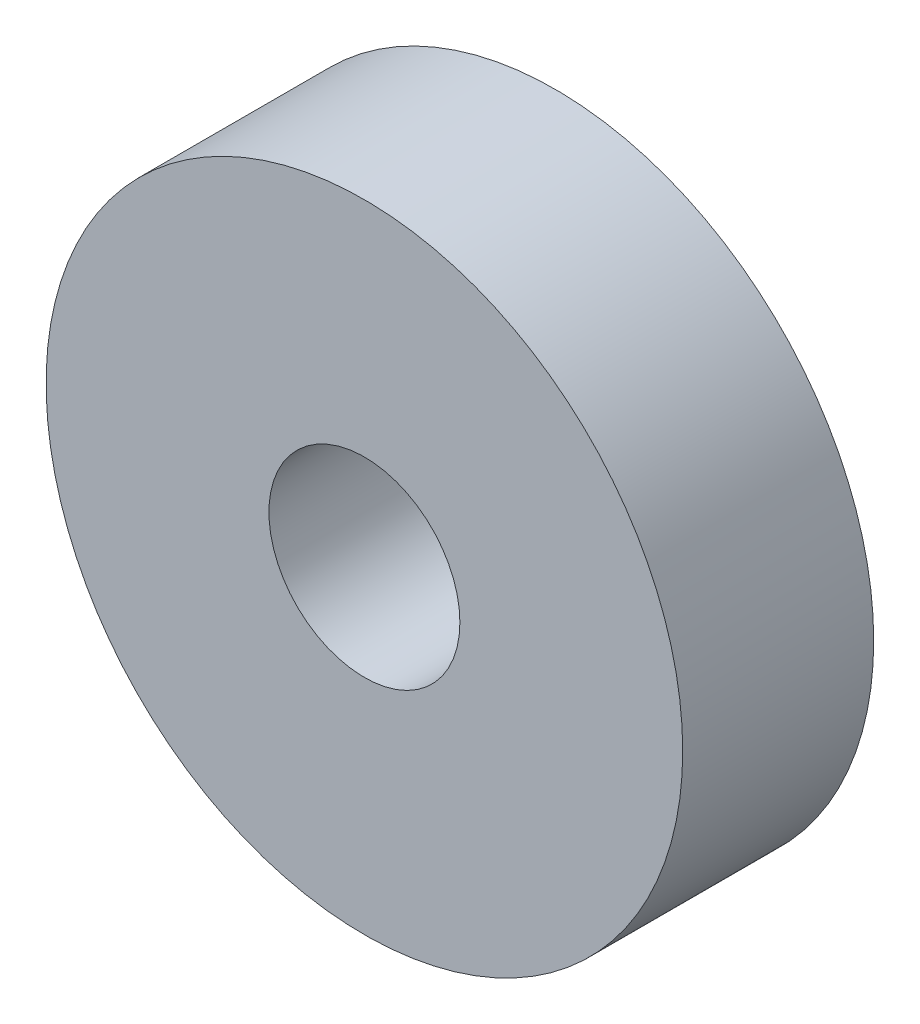
SolidWorks part; units mm, degrees
material "Stainless Steel (ferritic)"
ref_plane "Front Plane" through (0, 0, 0) normal (0, 0, 1) x (1, 0, 0)
ref_plane "Top Plane" through (0, 0, 0) normal (0, 1, 0) x (1, 0, 0)
ref_plane "Right Plane" through (0, 0, 0) normal (1, 0, 0) x (0, 0, -1)
sketch "Sketch1" plane through (0, 0, 0) normal (0, 0, 1) x (1, 0, 0)
  circle A0 centre (0, 0) radius 10
  circle A1 centre (0, 0) radius 3
  dimension "D1" = 20
  dimension "D2" = 6
extrude "Boss-Extrude1" add sketch "Sketch1" along normal blind 6
